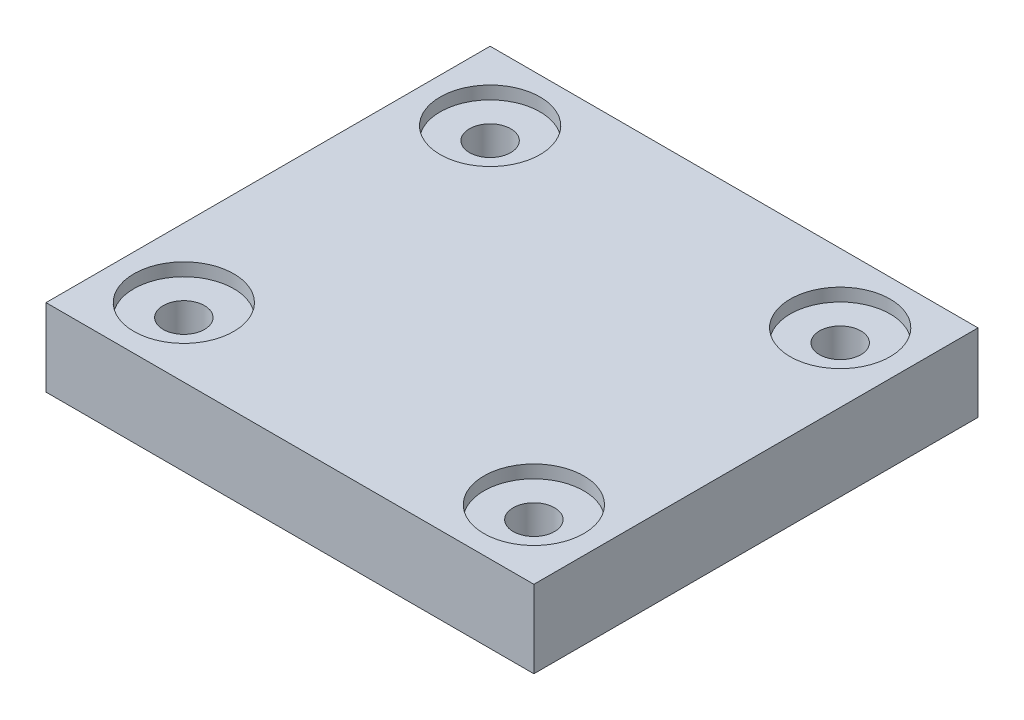
SolidWorks part; units mm, degrees
ref_plane "Front Plane" through (0, 0, 0) normal (0, 0, 1) x (1, 0, 0)
ref_plane "Top Plane" through (0, 0, 0) normal (0, 1, 0) x (1, 0, 0)
ref_plane "Right Plane" through (0, 0, 0) normal (1, 0, 0) x (0, 0, -1)
sketch "Sketch1" plane through (0, 0, 0) normal (0, 1, 0) x (1, 0, 0)
  line L0 (-14.16, -12.89) -> (-14.16, 12.89)
  line L1 (-10.16, -8.89) -> (10.16, -8.89) construction
  line L2 (-10.16, -8.89) -> (-10.16, 8.89) construction
  line L3 (-10.16, 8.89) -> (10.16, 8.89) construction
  line L4 (10.16, -8.89) -> (10.16, 8.89) construction
  line L5 (-10.16, -8.89) -> (10.16, 8.89) construction
  line L6 (-10.16, 8.89) -> (10.16, -8.89) construction
  line L7 (-14.16, 12.89) -> (14.16, 12.89)
  line L8 (14.16, -12.89) -> (14.16, 12.89)
  line L9 (-14.16, -12.89) -> (14.16, -12.89)
  circle A0 centre (-10.16, 8.89) radius 1.2
  circle A1 centre (10.16, 8.89) radius 1.2
  circle A2 centre (10.16, -8.89) radius 1.2
  circle A3 centre (-10.16, -8.89) radius 1.2
  point P0 (0, 0)
  dimension "D4" = 2.4
  dimension "D1" = 17.78
  dimension "D2" = 20.32
  dimension "D3" = 4
extrude "Boss-Extrude1" add sketch "Sketch1" along normal blind 5
sketch "Sketch3" plane through (0, 5, 0) normal (0, 1, 0) x (1, 0, 0)
  circle A0 centre (-10.16, 8.89) radius 2.9
  circle A1 centre (10.16, 8.89) radius 2.9
  circle A2 centre (10.16, -8.89) radius 2.9
  circle A3 centre (-10.16, -8.89) radius 2.9
  dimension "D1" = 5.8
extrude "Cut-Extrude1" cut sketch "Sketch3" against normal blind 0.75
chamfer "Chamfer1" distance 0.5 angle 45 8 edges at (-10.16, 0, 10.09) (10.16, 0, 10.09) (10.16, 0, -7.69) (-10.16, 0, -7.69) (14.16, 0, 0) (0, 0, -12.89) (-14.16, 0, 0) (0, 0, 12.89)
equation "\"D1@Sketch1\"=0.7in"
equation "\"D2@Sketch1\"=0.8in"
